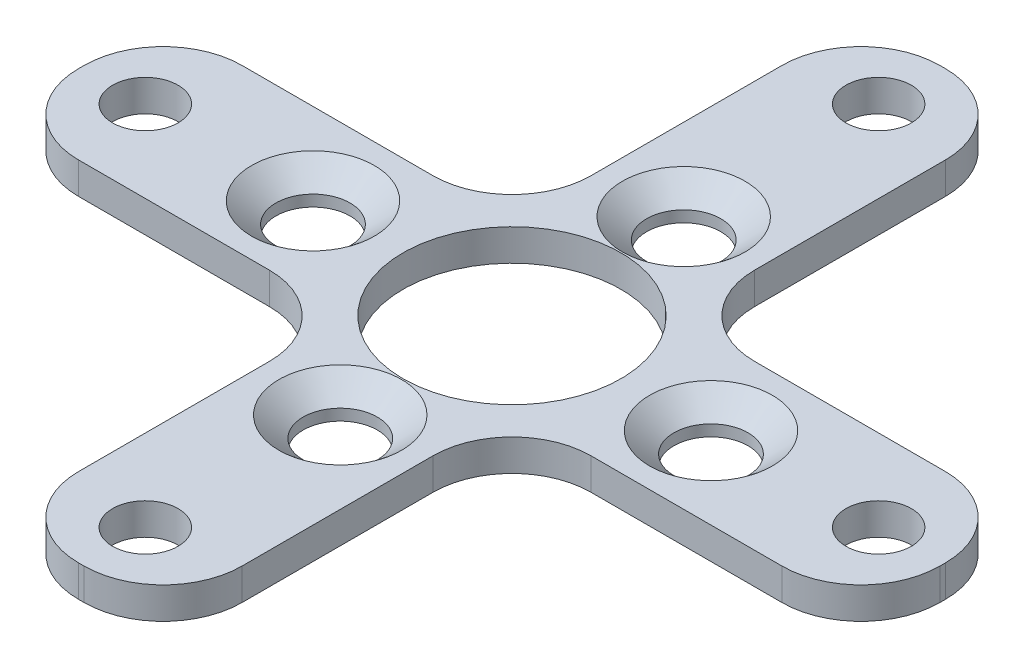
SolidWorks part; units mm, degrees
material "1060 Alloy"
ref_plane "Front" through (0, 0, 0) normal (0, 0, 1) x (1, 0, 0)
ref_plane "Top" through (0, 0, 0) normal (0, 1, 0) x (1, 0, 0)
ref_plane "Right" through (0, 0, 0) normal (1, 0, 0) x (0, 0, -1)
sketch "Sketch1" plane through (0, 0, 0) normal (0, 1, 0) x (1, 0, 0)
  line L0 (-3.81, 7.493) -> (-3.81, 16.383)
  line L1 (-0.127, -20.066) -> (0.127, -20.066)
  line L2 (-3.81, -16.383) -> (-3.81, -7.493)
  line L3 (-0.127, 20.066) -> (0.127, 20.066)
  line L4 (3.81, -16.383) -> (3.81, -7.493)
  line L5 (0, 17.0815) -> (0, -17.0815) construction
  line L6 (17.0815, 0) -> (-17.0815, 0) construction
  line L7 (-16.383, -3.81) -> (-7.493, -3.81)
  line L8 (-20.066, -0.127) -> (-20.066, 0.127)
  line L9 (-16.383, 3.81) -> (-7.493, 3.81)
  line L10 (20.066, -0.127) -> (20.066, 0.127)
  line L14 (7.493, 3.81) -> (16.383, 3.81)
  line L15 (3.81, 7.493) -> (3.81, 16.383)
  line L18 (7.493, -3.81) -> (16.383, -3.81)
  circle A0 centre (0, 0) radius 5.08
  arc A1 (-20.066, 0.127) -> (-16.383, 3.81) centre (-16.383, 0.127) cw
  arc A2 (-16.383, -3.81) -> (-20.066, -0.127) centre (-16.383, -0.127) cw
  arc A3 (-7.493, -3.81) -> (-3.81, -7.493) centre (-7.493, -7.493) cw
  arc A4 (3.81, -7.493) -> (7.493, -3.81) centre (7.493, -7.493) cw
  arc A5 (16.383, -3.81) -> (20.066, -0.127) centre (16.383, -0.127) ccw
  arc A6 (16.383, 3.81) -> (20.066, 0.127) centre (16.383, 0.127) cw
  arc A7 (7.493, 3.81) -> (3.81, 7.493) centre (7.493, 7.493) cw
  arc A8 (0.127, 20.066) -> (3.81, 16.383) centre (0.127, 16.383) cw
  arc A9 (-3.81, 16.383) -> (-0.127, 20.066) centre (-0.127, 16.383) cw
  arc A10 (-3.81, 7.493) -> (-7.493, 3.81) centre (-7.493, 7.493) cw
  arc A11 (0.127, -20.066) -> (3.81, -16.383) centre (0.127, -16.383) ccw
  arc A12 (-0.127, -20.066) -> (-3.81, -16.383) centre (-0.127, -16.383) cw
  circle A13 centre (0, 17.0815) radius 1.524
  circle A14 centre (17.0815, 0) radius 1.524
  circle A15 centre (-17.0815, 0) radius 1.524
  circle A16 centre (0, -17.0815) radius 1.524
  point P23 (3.81, -3.81)
  point P30 (3.81, 3.81)
  point P42 (0, 20.066)
  point P43 (20.066, 0)
  dimension "D1" = 3.683
  dimension "D2" = 3.683
  dimension "D5" = 10.16
  dimension "D9" = 3.048
  dimension "D3" = 7.62
  dimension "D4" = 7.62
  dimension "D6" = 40.132
  dimension "D7" = 40.132
  dimension "D8" = 34.163
extrude "Boss-Extrude1" add sketch "Sketch1" along normal blind 1.4732
hole_wizard "CSK for #4 Flat Head Machine Screw (100)2" positions "Sketch2" profile "Sketch3" countersink size "#4" standard "ANSI Inch"
sketch "Sketch2" plane through (0, 1.4732, 0) normal (0, 1, 0) x (1, 0, 0)
  line L0 (-9.271, 0) -> (9.271, 0) construction
  line L2 (0, 8.001) -> (0, -8.001) construction
  point P0 (0, 8.001)
  point P2 (0, -8.001)
  point P4 (9.271, 0)
  point P6 (-9.271, 0)
  dimension "D1" = 18.542
  dimension "D2" = 16.002
sketch "Sketch3" plane through (0, 1.4732, -8.001) normal (1, 0, 0) x (0, 0, 1)
  line L0 (0, 0) -> (0, 4.4871)
  line L1 (0, 4.4871) -> (1.7272, 3.4493)
  line L2 (1.7272, 3.4493) -> (1.7272, 0.9484)
  line L3 (1.7272, 0.9484) -> (2.8575, 0)
  line L5 (2.8575, 0) -> (0, 0)
  line L6 (-1.7272, 0.9484) -> (-2.8575, 0) construction
  line L10 (0, 4.4871) -> (-1.7272, 3.4493) construction
  line L11 (0, -6.35) -> (0, 107.95) construction
  dimension "Hole Dia." = 3.4544
  dimension "Hole Depth" = 3.4493
  dimension "Near C'Sink Dia." = 5.715
  dimension "Near C'Sink Angle" = 100
  dimension "Drill Angle" = 118
